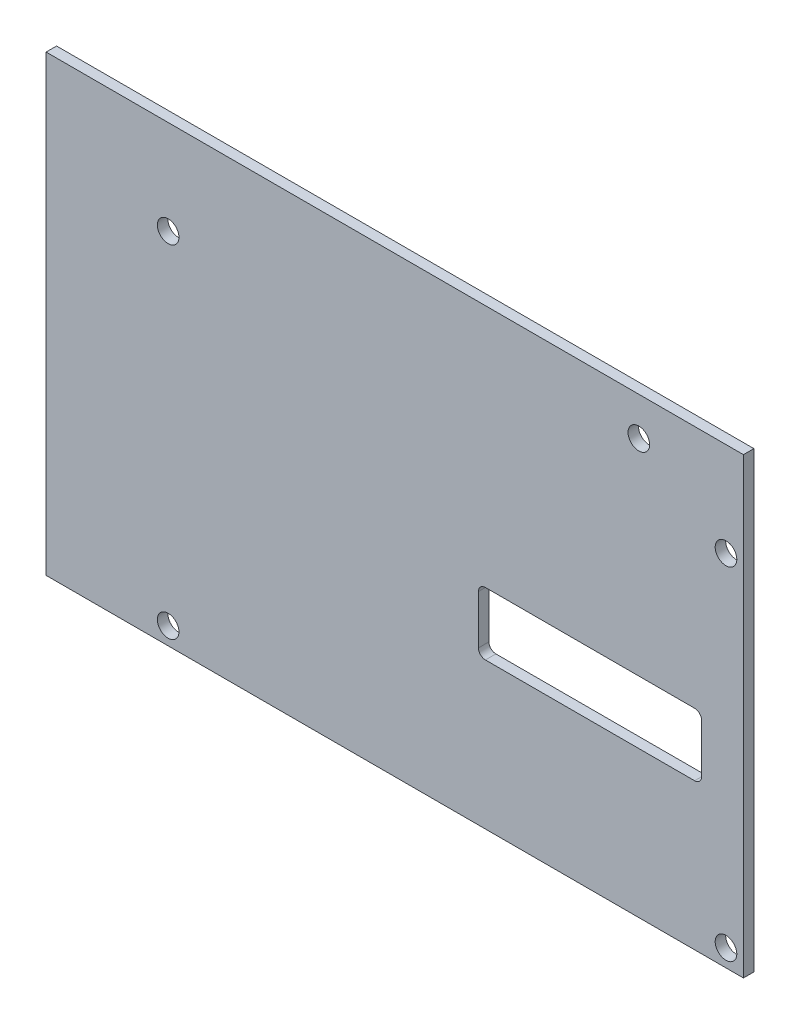
SolidWorks part; units mm, degrees
ref_plane "Спереди" through (0, 0, 0) normal (0, 0, 1) x (1, 0, 0)
ref_plane "Сверху" through (0, 0, 0) normal (0, 1, 0) x (1, 0, 0)
ref_plane "Справа" through (0, 0, 0) normal (1, 0, 0) x (0, 0, -1)
sketch "Эскиз1" plane through (0, 0, 0) normal (0, 0, 1) x (1, 0, 0)
  line L0 (0, 65) -> (100, 65)
  line L1 (0, 0) -> (100, 0)
  line L2 (0, 0) -> (0, 65)
  line L4 (100, 0) -> (100, 65)
  line L9 (63, 30) -> (93, 30)
  line L10 (62, 29) -> (62, 22)
  line L11 (63, 21) -> (93, 21)
  line L12 (94, 29) -> (94, 22)
  circle A0 centre (17.5, 51.5) radius 1.55
  circle A1 centre (97.5, 51.5) radius 1.55
  circle A2 centre (97.5, 2.5) radius 1.55
  circle A3 centre (17.5, 2.5) radius 1.55
  arc A4 (63, 30) -> (62, 29) centre (63, 29) ccw
  arc A5 (94, 29) -> (93, 30) centre (93, 29) ccw
  circle A6 centre (85, 59.5) radius 1.55
  arc A8 (94, 22) -> (93, 21) centre (93, 22) cw
  arc A9 (63, 21) -> (62, 22) centre (63, 22) cw
  dimension "D6" = 49
  dimension "D8" = 65
  dimension "D9" = 2.5
  dimension "D10" = 3.1
  dimension "D2" = 80
  dimension "D5" = 2.5
  dimension "D11" = 1
  dimension "D12" = 32
  dimension "D13" = 9
  dimension "D14" = 6
  dimension "D4" = 12.5
  dimension "D7" = 8
  dimension "D3" = 100
  dimension "D15" = 21
extrude "Бобышка-Вытянуть1" add sketch "Эскиз1" along normal blind 1.5
